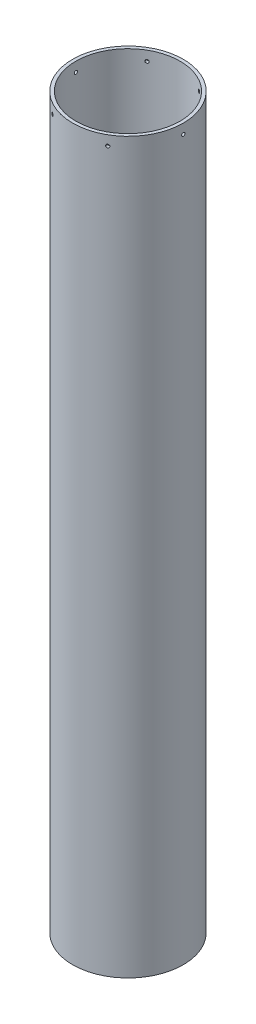
SolidWorks part; units mm, degrees
ref_plane "Front Plane" through (0, 0, 0) normal (0, 0, 1) x (1, 0, 0)
ref_plane "Top Plane" through (0, 0, 0) normal (0, 1, 0) x (1, 0, 0)
ref_plane "Right Plane" through (0, 0, 0) normal (1, 0, 0) x (0, 0, -1)
sketch "Sketch1" plane through (0, 0, 0) normal (0, 1, 0) x (1, 0, 0)
  circle A4 centre (0, 0) radius 50.8
  circle A5 centre (0, 0) radius 53.975
  point P0 (0, 0)
  dimension "D1" = 101.6
  dimension "D2" = 3.175
extrude "Boss-Extrude1" add sketch "Sketch1" along normal blind 711.2
sketch "Sketch2" plane through (0, 0, 0) normal (1, 0, 0) x (0, 0, -1)
  line L0 (0, 711.2) -> (0, 701.675) construction
  line L1 (50.8, 711.2) -> (-50.8, 711.2) construction
  circle A0 centre (0, 701.675) radius 1.5875
  dimension "D2" = 3.175
  dimension "D1" = 9.525
extrude "Cut-Extrude1" cut sketch "Sketch2" against normal through all both and the other way through all
pattern_circular "CirPattern1" count 3 over 360 about axis through (0, 711.2, 0) along (0, 1, 0) of "Cut-Extrude1"
